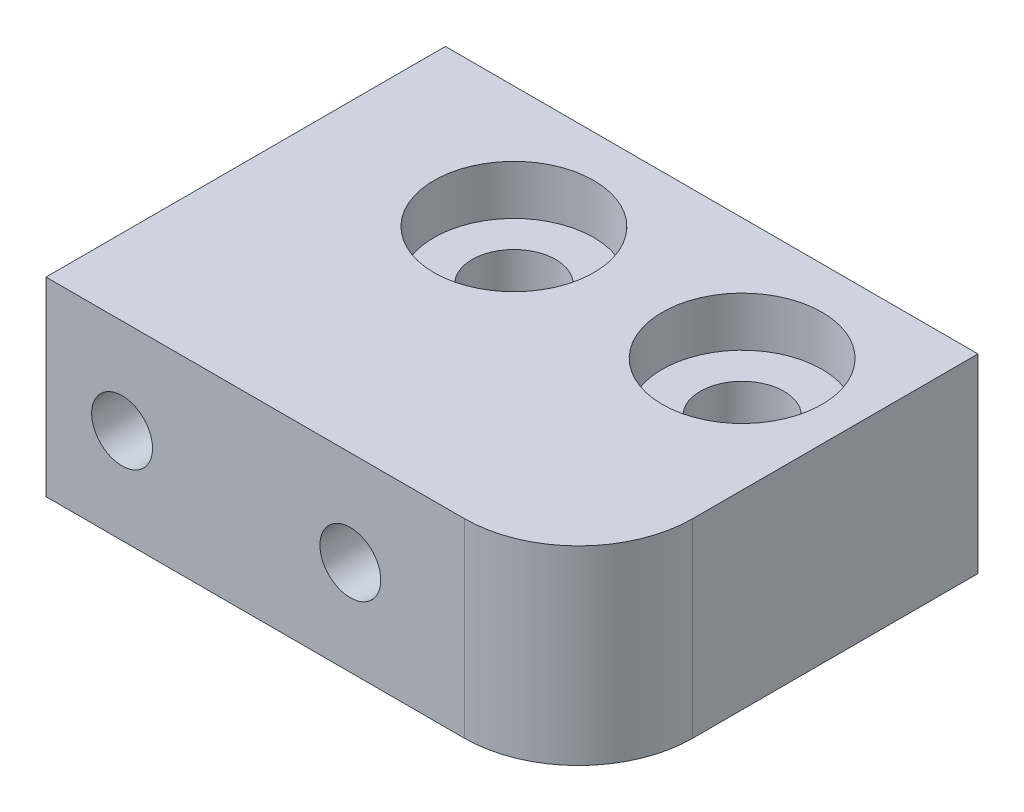
SolidWorks part; units mm, degrees
material "ﾎﾟﾘｵｷｼﾒﾁﾚﾝ(POM)ｱｾﾀｰﾙ共重合体"
ref_plane "正面" through (0, 0, 0) normal (0, 0, 1) x (1, 0, 0)
ref_plane "平面" through (0, 0, 0) normal (0, 1, 0) x (1, 0, 0)
ref_plane "右側面" through (0, 0, 0) normal (1, 0, 0) x (0, 0, -1)
sketch "Sketch1" plane through (0, 0, 0) normal (0, 1, 0) x (1, 0, 0)
  line L1 (-7, 5.25) -> (7, 5.25)
  line L2 (-7, 5.25) -> (-7, -5.25)
  line L3 (-7, -5.25) -> (7, -5.25)
  line L4 (7, 5.25) -> (7, -5.25)
  line L5 (-7, 5.25) -> (7, -5.25) construction
  line L6 (-7, -5.25) -> (7, 5.25) construction
  point P0 (0, 0)
  dimension "D1" = 10.5
  dimension "D2" = 14
extrude "Boss-Extrude1" add sketch "Sketch1" along normal blind 5
sketch "Sketch2" plane through (0, 0, 5.25) normal (0, 0, 1) x (1, 0, 0)
  line L1 (-7, 5) -> (-5, 5)
  line L2 (-7, 5) -> (-7, 2.5)
  line L3 (-7, 2.5) -> (-5, 2.5)
  line L4 (-5, 5) -> (-5, 2.5)
  line L5 (7, 5) -> (1, 5)
  line L6 (7, 5) -> (7, 2.5)
  line L7 (7, 2.5) -> (1, 2.5)
  line L8 (1, 5) -> (1, 2.5)
  dimension "D1" = 2
  dimension "D2" = 2.5
  dimension "D3" = 8
  dimension "D4" = 2.5
sketch "Sketch6" plane through (0, 5, 0) normal (0, 1, 0) x (1, 0, 0)
  line L1 (-7, 5.25) -> (-2, 5.25)
  line L2 (-7, 5.25) -> (-7, 2.25)
  line L3 (-7, 2.25) -> (-2, 2.25)
  line L4 (-2, 5.25) -> (-2, 2.25)
  line L5 (7, 5.25) -> (4, 5.25)
  line L6 (7, 5.25) -> (7, 2.25)
  line L7 (7, 2.25) -> (4, 2.25)
  line L8 (4, 5.25) -> (4, 2.25)
  dimension "D1" = 5
  dimension "D2" = 11
  dimension "D3" = 3
  dimension "D4" = 3
hole_wizard "Hole1" positions "Sketch8" profile "Sketch9" legacy end condition through all
sketch "Sketch8" plane through (0, 5, 0) normal (0, 1, 0) x (1, 0, 0)
  line L0 (7, 5.25) -> (-7, 5.25) construction
  point P0 (-2, 2.05)
  point P3 (4, 2.05)
  dimension "D1" = 3.2
  dimension "D2" = 3.2
sketch "Sketch9" plane through (-2, 5, -2.05) normal (1, 0, 0) x (0, 0, 1)
  line L0 (0, 0) -> (0, 5)
  line L1 (0, 5) -> (1.1, 5)
  line L2 (1.1, 5) -> (1.1, 1.3)
  line L3 (1.1, 1.3) -> (2.1, 1.3)
  line L4 (2.1, 1.3) -> (2.1, 0)
  line L5 (2.1, 0) -> (0, 0)
  line L6 (0, 110) -> (0, -10) construction
  dimension "Diameter" = 2.2
  dimension "Depth" = 5
  dimension "C-Bore Diameter" = 4.2
  dimension "C-Bore Depth" = 1.3
fillet "ﾌｨﾚｯﾄ2" radius 3 1 edges at (7, 2.5, 5.25)
sketch "ｽｹｯﾁ6" plane through (0, 0, 5.25) normal (0, 0, 1) x (1, 0, 0)
  line L0 (-7, 5) -> (-7, 0) construction
  line L1 (-7, 0) -> (4, 0) construction
  point P0 (-5, 2.5)
  point P1 (1, 2.5)
  dimension "D1" = 2
  dimension "D2" = 8
  dimension "D3" = 2.5
  dimension "D4" = 2.5
hole_wizard "M2x0.4 ねじ穴5" positions "3Dｽｹｯﾁ4" profile "ｽｹｯﾁ7" tap size "M2x0.4" standard "JIS" end condition through all
sketch3d "3Dｽｹｯﾁ4"
  point P0 (-5, 2.5, 5.25)
  point P3 (1, 2.5, 5.25)
sketch "ｽｹｯﾁ7" plane through (-5, 2.5, 5.25) normal (1, 0, 0) x (0, -1, 0)
  line L0 (0, 0) -> (0, 10.5)
  line L1 (0, 10.5) -> (0.8, 10.5)
  line L2 (0.8, 10.5) -> (0.8, 0)
  line L5 (0.8, 0) -> (0, 0)
  line L11 (0, -6.35) -> (0, 107.95) construction
  dimension "次ｻｰﾌｪｽまでのねじ下穴ﾄﾞﾘﾙ直径" = 1.6
  dimension "次ｻｰﾌｪｽまでのねじ下穴ﾄﾞﾘﾙの深さ" = 10.5
cosmetic thread "穴のねじ山1" parameters "D1"=10.5, "D2"=2
cosmetic thread "穴のねじ山2" parameters "D1"=10.5, "D2"=2
sketch "Sketch11" plane through (0, 5, 0) normal (0, 1, 0) x (1, 0, 0)
  point P0 (-2, 2.05)
  point P1 (4, 2.05)
